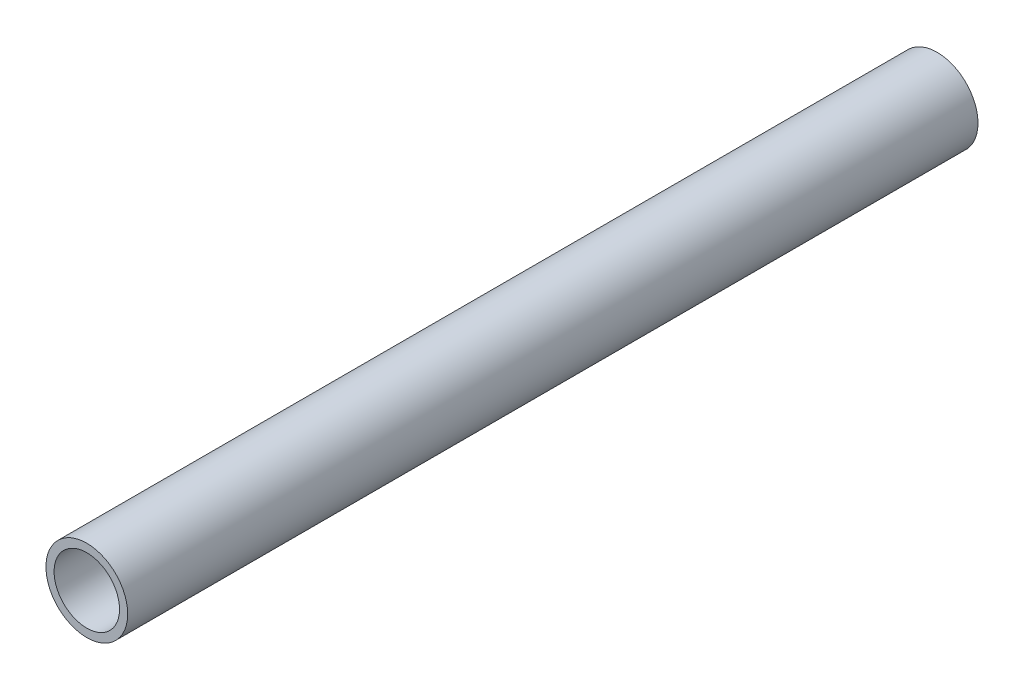
SolidWorks part; units mm, degrees
ref_plane "Front Plane" through (0, 0, 0) normal (0, 0, 1) x (1, 0, 0)
ref_plane "Top Plane" through (0, 0, 0) normal (0, 1, 0) x (1, 0, 0)
ref_plane "Right Plane" through (0, 0, 0) normal (1, 0, 0) x (0, 0, -1)
sketch "Sketch1" plane through (0, 0, 0) normal (0, 0, 1) x (1, 0, 0)
  circle A0 centre (0, 0) radius 1
  circle A1 centre (0, 0) radius 1.25
  dimension "D1" = 2
  dimension "D2" = 2.5
extrude "Boss-Extrude1" add sketch "Sketch1" along normal blind 26
